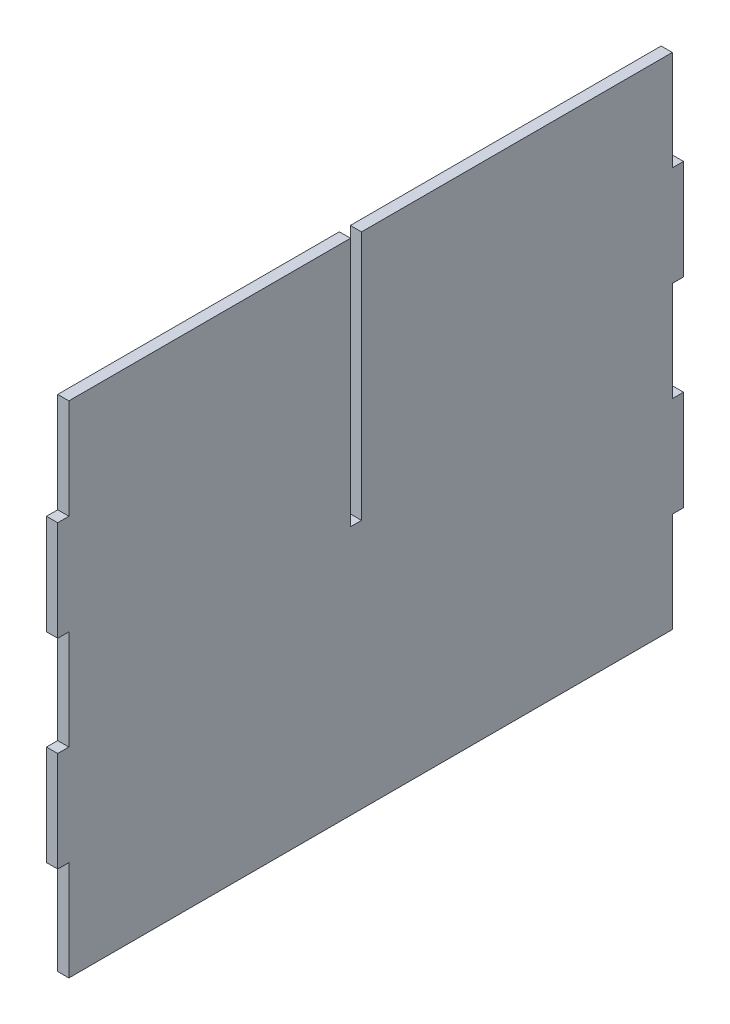
SolidWorks part; units mm, degrees
ref_plane "Front Plane" through (0, 0, 0) normal (0, 0, 1) x (1, 0, 0)
ref_plane "Top Plane" through (0, 0, 0) normal (0, 1, 0) x (1, 0, 0)
ref_plane "Right Plane" through (0, 0, 0) normal (1, 0, 0) x (0, 0, -1)
sketch "Sketch1" plane through (0, 0, 0) normal (1, 0, 0) x (0, 0, -1)
  line L0 (-7.0375, 130) -> (142.9875, 130)
  line L1 (-148.3875, -111.325) -> (142.9875, -111.325)
  line L2 (-148.3875, -111.325) -> (-148.3875, 130)
  line L3 (-148.3875, 130) -> (-12.4375, 130)
  line L4 (142.9875, -111.325) -> (142.9875, 130)
  line L8 (-12.4375, 130) -> (-12.4375, 9.3375)
  line L9 (-12.4375, 9.3375) -> (-7.0375, 9.3375)
  line L10 (-7.0375, 130) -> (-7.0375, 9.3375)
  line L11 (-2.7, 18.675) -> (-2.7, -111.325) construction
  line L12 (142.9875, 81.735) -> (148.3875, 81.735)
  line L13 (142.9875, 81.735) -> (142.9875, 33.47)
  line L14 (142.9875, 33.47) -> (148.3875, 33.47)
  line L15 (148.3875, 81.735) -> (148.3875, 33.47)
  line L16 (142.9875, -14.795) -> (148.3875, -14.795)
  line L17 (142.9875, -14.795) -> (142.9875, -63.06)
  line L18 (142.9875, -63.06) -> (148.3875, -63.06)
  line L19 (148.3875, -14.795) -> (148.3875, -63.06)
  line L20 (-148.3875, -63.06) -> (-153.7875, -63.06)
  line L21 (-153.7875, -14.795) -> (-153.7875, -63.06)
  line L22 (-148.3875, -14.795) -> (-153.7875, -14.795)
  line L23 (-148.3875, 33.47) -> (-153.7875, 33.47)
  line L24 (-153.7875, 81.735) -> (-153.7875, 33.47)
  line L25 (-148.3875, 81.735) -> (-153.7875, 81.735)
  point P0 (0, 0)
  dimension "D1" = 241.325
  dimension "D2" = 5.4
  dimension "D3" = 5.4
  dimension "D4" = 5.4
  dimension "D5" = 48.265
  dimension "D6" = 48.265
  dimension "D7" = 48.265
  dimension "D8" = 48.265
  dimension "D9" = 135.95
  dimension "D10" = 150.025
  dimension "D11" = 48.265
  dimension "D12" = 5.4
  dimension "D13" = 48.265
  dimension "D14" = 48.265
  dimension "D15" = 48.265
  dimension "D16" = 120.6625
  dimension "D17" = 120.6625
extrude "Boss-Extrude2" add sketch "Sketch1" along normal blind 5.4 contours L0 L10 L9 L8 L3 L2 L1 L4 | L2 L25 L24 L23 | L2 L22 L21 L20 | L15 L12 L4 L14 | L19 L16 L4 L18 | L10 L11 L1 L4 L0
sketch "Sketch2" plane through (5.4, 0, 0) normal (1, 0, 0) x (0, 0, -1)
  line L48 (-148.4281, -111.3656) -> (143.0281, -111.3656)
  line L49 (143.0281, -111.3656) -> (143.0281, -63.1006)
  line L50 (143.0281, -63.1006) -> (148.4281, -63.1006)
  line L51 (148.4281, -63.1006) -> (148.4281, -14.7544)
  line L52 (148.4281, -14.7544) -> (143.0281, -14.7544)
  line L53 (143.0281, -14.7544) -> (143.0281, 33.4294)
  line L54 (143.0281, 33.4294) -> (148.4281, 33.4294)
  line L55 (148.4281, 33.4294) -> (148.4281, 81.7756)
  line L56 (148.4281, 81.7756) -> (143.0281, 81.7756)
  line L57 (143.0281, 81.7756) -> (143.0281, 130.0406)
  line L58 (143.0281, 130.0406) -> (-7.0781, 130.0406)
  line L59 (-7.0781, 130.0406) -> (-7.0781, 9.3781)
  line L60 (-7.0781, 9.3781) -> (-12.3969, 9.3781)
  line L61 (-12.3969, 9.3781) -> (-12.3969, 130.0406)
  line L62 (-12.3969, 130.0406) -> (-148.4281, 130.0406)
  line L63 (-148.4281, 130.0406) -> (-148.4281, 81.7756)
  line L64 (-148.4281, 81.7756) -> (-153.8281, 81.7756)
  line L65 (-153.8281, 81.7756) -> (-153.8281, 33.4294)
  line L66 (-153.8281, 33.4294) -> (-148.4281, 33.4294)
  line L67 (-148.4281, 33.4294) -> (-148.4281, -14.7544)
  line L68 (-148.4281, -14.7544) -> (-153.8281, -14.7544)
  line L69 (-153.8281, -14.7544) -> (-153.8281, -63.1006)
  line L70 (-153.8281, -63.1006) -> (-148.4281, -63.1006)
  line L71 (-148.4281, -63.1006) -> (-148.4281, -111.3656)
  line L72 (-148.4281, -111.3656) -> (143.0281, -111.3656)
  line L73 (143.0281, -111.3656) -> (143.0281, -63.1006)
  line L74 (143.0281, -63.1006) -> (148.4281, -63.1006)
  line L75 (148.4281, -63.1006) -> (148.4281, -14.7544)
  line L76 (148.4281, -14.7544) -> (143.0281, -14.7544)
  line L77 (143.0281, -14.7544) -> (143.0281, 33.4294)
  line L78 (143.0281, 33.4294) -> (148.4281, 33.4294)
  line L79 (148.4281, 33.4294) -> (148.4281, 81.7756)
  line L80 (148.4281, 81.7756) -> (143.0281, 81.7756)
  line L81 (143.0281, 81.7756) -> (143.0281, 130.0406)
  line L82 (143.0281, 130.0406) -> (-7.0781, 130.0406)
  line L83 (-7.0781, 130.0406) -> (-7.0781, 9.3781)
  line L84 (-7.0781, 9.3781) -> (-12.3969, 9.3781)
  line L85 (-12.3969, 9.3781) -> (-12.3969, 130.0406)
  line L86 (-12.3969, 130.0406) -> (-148.4281, 130.0406)
  line L87 (-148.4281, 130.0406) -> (-148.4281, 81.7756)
  line L88 (-148.4281, 81.7756) -> (-153.8281, 81.7756)
  line L89 (-153.8281, 81.7756) -> (-153.8281, 33.4294)
  line L90 (-153.8281, 33.4294) -> (-148.4281, 33.4294)
  line L91 (-148.4281, 33.4294) -> (-148.4281, -14.7544)
  line L92 (-148.4281, -14.7544) -> (-153.8281, -14.7544)
  line L93 (-153.8281, -14.7544) -> (-153.8281, -63.1006)
  line L94 (-153.8281, -63.1006) -> (-148.4281, -63.1006)
  line L95 (-148.4281, -63.1006) -> (-148.4281, -111.3656)
  dimension "D1" = 0.0406
extrude "Boss-Extrude3" add sketch "Sketch2" against normal up to surface (5.4 mm away) up to face at (0, 19.3927, 3.8729)
